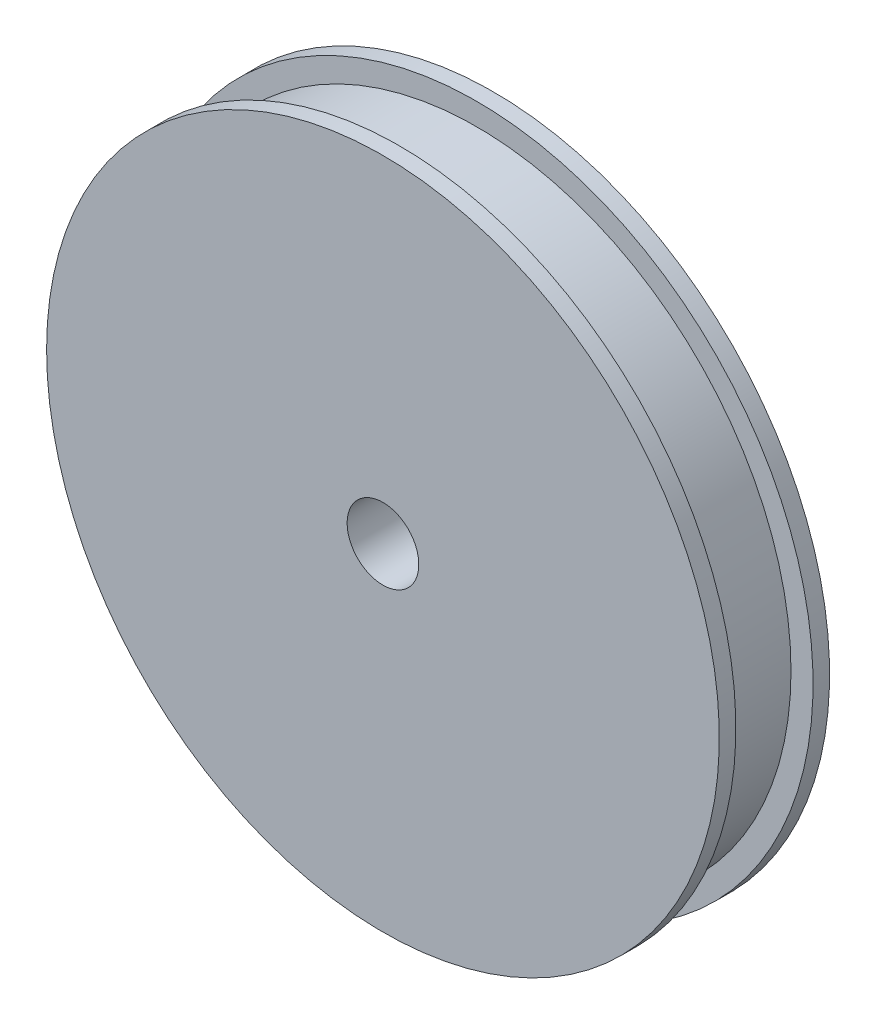
SolidWorks part; units mm, degrees
ref_plane "Спереди" through (0, 0, 0) normal (0, 0, 1) x (1, 0, 0)
ref_plane "Сверху" through (0, 0, 0) normal (0, 1, 0) x (1, 0, 0)
ref_plane "Справа" through (0, 0, 0) normal (1, 0, 0) x (0, 0, -1)
sketch "Эскиз2" plane through (0, 0, 0) normal (1, 0, 0) x (0, 0, -1)
  line L0 (0, 0) -> (0, 30.5)
  line L1 (0, 30.5) -> (1.5, 30.5)
  line L2 (1.5, 30.5) -> (1.5, 28.5)
  line L3 (1.5, 28.5) -> (8.5, 28.5)
  line L4 (8.5, 28.5) -> (8.5, 30.5)
  line L5 (8.5, 30.5) -> (10, 30.5)
  line L6 (10, 30.5) -> (10, 0)
  line L7 (10, 0) -> (0, 0)
  line L8 (5, 0) -> (5, 28.5) construction
  dimension "D1" = 2
  dimension "D2" = 28.5
  dimension "D3" = 10
  dimension "D4" = 7
revolve "Повернуть1" add sketch "Эскиз2" angle 360 about L7
sketch "Эскиз3" plane through (0, 0, -10) normal (0, 0, -1) x (-1, 0, 0)
  circle A0 centre (0, 0) radius 15
  dimension "D1" = 30
extrude "Бобышка-Вытянуть1" add sketch "Эскиз3" along normal blind 7
sketch "Эскиз4" plane through (0, 0, -17) normal (0, 0, -1) x (-1, 0, 0)
  circle A0 centre (0, 0) radius 3.25
  dimension "D1" = 6.5
extrude "Вырез-Вытянуть1" cut sketch "Эскиз4" against normal through all
sketch "Эскиз5" plane through (0, 0, 0) normal (0, 0, 1) x (1, 0, 0)
  line L0 (0, 0) -> (28.5, 0) construction
  circle A0 centre (0, 0) radius 28.5 construction
  circle A1 centre (0, 0) radius 28.5 construction
ref_plane "Плоскость1" through (28.5, 0, 0) normal (1, 0, 0) x (0, 0, -1)
sketch "Эскиз6" plane through (0, 0, 0) normal (1, 0, 0) x (0, 0, -1)
  line L0 (8.5, 28.5) -> (8.5, -28.5) construction
  line L1 (8.5, 28.5) -> (8.5, -28.5) construction
  line L2 (1.5, -28.5) -> (1.5, 28.5) construction
  line L3 (1.5, -28.5) -> (1.5, 28.5) construction
  line L4 (1.5, 28.5) -> (8.5, 28.5) construction
  line L5 (1.5, -28.5) -> (8.5, -28.5) construction
  line L6 (5, 28.5) -> (5, -28.5) construction
